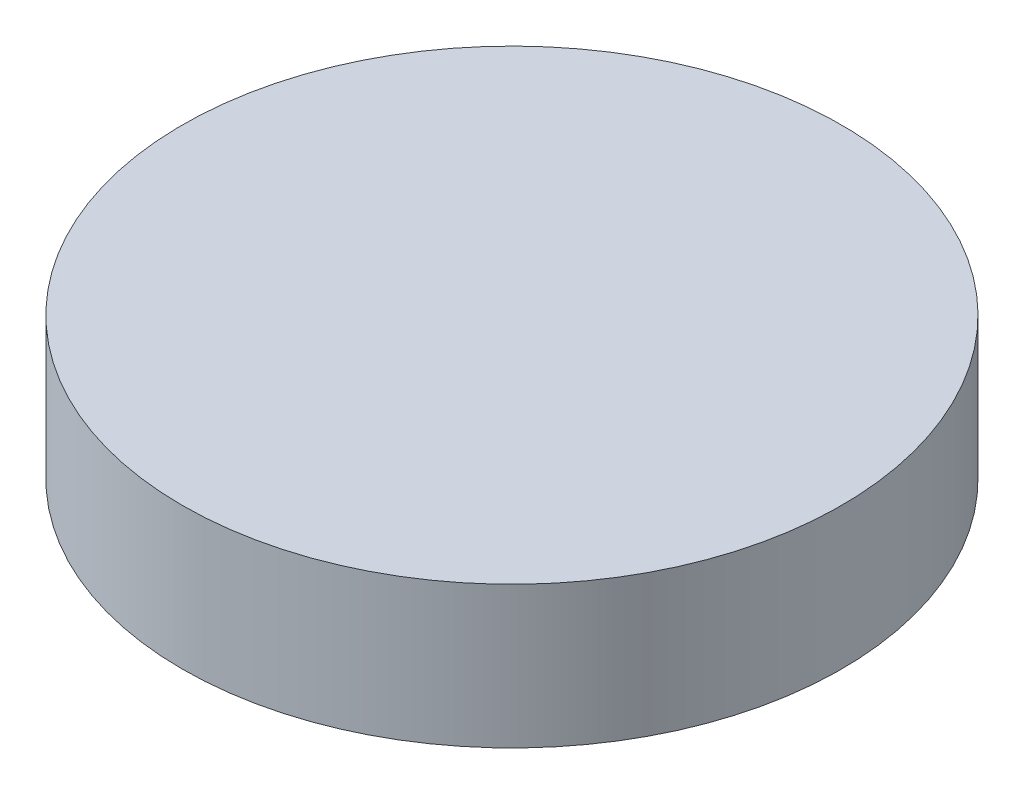
SolidWorks part; units mm, degrees
ref_plane "Front Plane" through (0, 0, 0) normal (0, 0, 1) x (1, 0, 0)
ref_plane "Top Plane" through (0, 0, 0) normal (0, 1, 0) x (1, 0, 0)
ref_plane "Right Plane" through (0, 0, 0) normal (1, 0, 0) x (0, 0, -1)
sketch "Sketch1" plane through (0, 0, 0) normal (0, 1, 0) x (1, 0, 0)
  circle A0 centre (0, 0) radius 20
  circle A1 centre (0, 0) radius 21.5
  dimension "D1" = 40
  dimension "D2" = 1.5
extrude "Boss-Extrude1" add sketch "Sketch1" along normal blind 7.5
sketch "Sketch2" plane through (0, 7.5, 0) normal (0, 1, 0) x (1, 0, 0)
  circle A0 centre (0, 0) radius 21.5
extrude "Boss-Extrude2" add sketch "Sketch2" along normal blind 1.75
